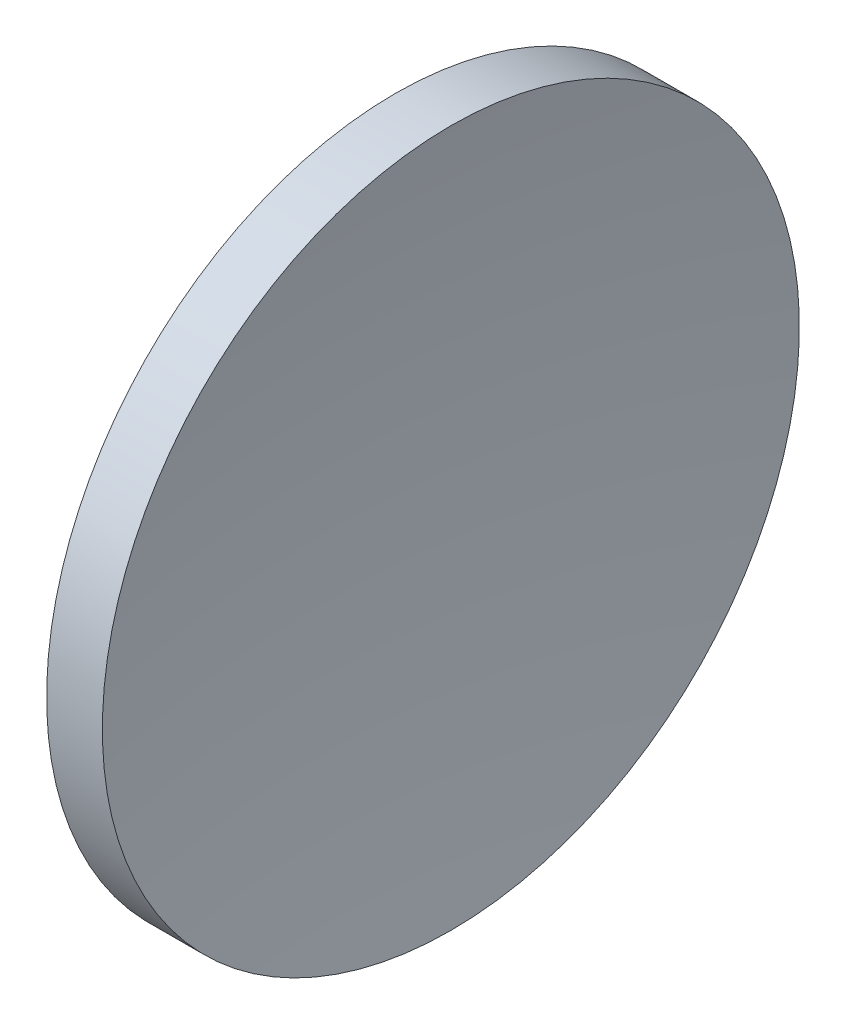
SolidWorks part; units mm, degrees
ref_plane "前视基准面" through (0, 0, 0) normal (0, 0, 1) x (1, 0, 0)
ref_plane "上视基准面" through (0, 0, 0) normal (0, 1, 0) x (1, 0, 0)
ref_plane "右视基准面" through (0, 0, 0) normal (1, 0, 0) x (0, 0, -1)
sketch "草图1" plane through (0, 0, 0) normal (0, 0, 1) x (1, 0, 0)
  line L0 (231.889, 130.4337) -> (271.8964, 130.4337) construction
  line L1 (248.1605, 155.4337) -> (252.158, 155.4337)
  line L2 (245.199, 130.4337) -> (250.199, 130.4337)
  arc A0 (248.1605, 155.4337) -> (245.199, 130.4337) centre (352.199, 130.4337) ccw
  arc A1 (252.158, 155.4337) -> (250.199, 130.4337) centre (410.699, 130.4337) ccw
revolve "旋转1" add sketch "草图1" angle 360 about L0
